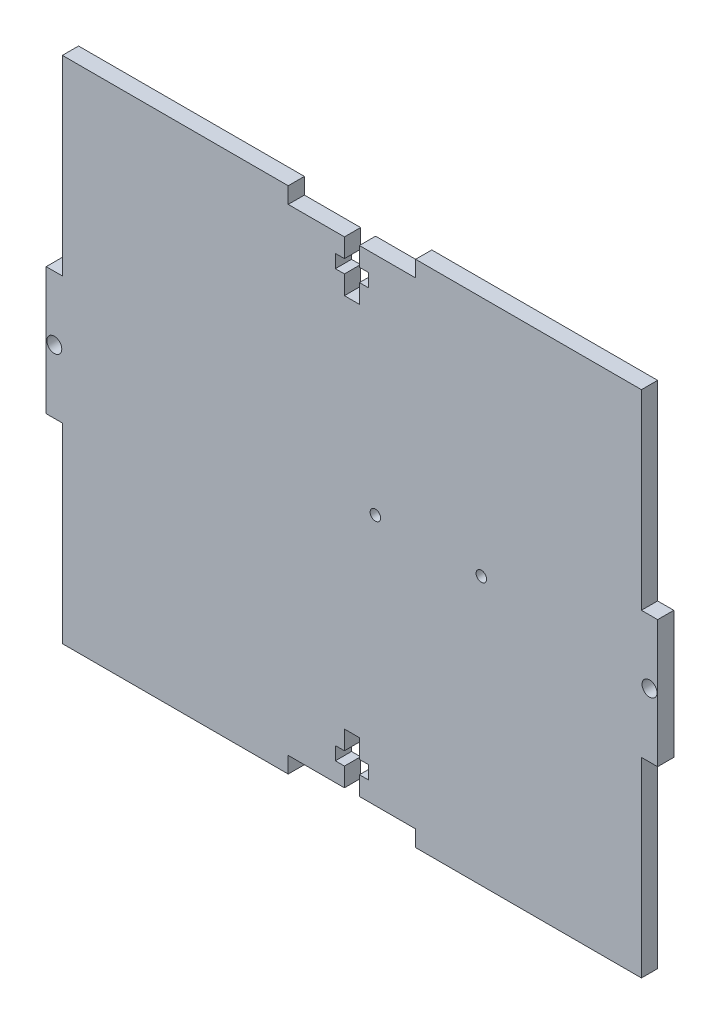
SolidWorks part; units mm, degrees
ref_plane "Front Plane" through (0, 0, 0) normal (0, 0, 1) x (1, 0, 0)
ref_plane "Top Plane" through (0, 0, 0) normal (0, 1, 0) x (1, 0, 0)
ref_plane "Right Plane" through (0, 0, 0) normal (1, 0, 0) x (0, 0, -1)
sketch "Sketch1" plane through (0, 0, 0) normal (0, 0, 1) x (1, 0, 0)
  line L0 (0, 50) -> (0, -50) construction
  line L1 (-56.825, 50) -> (56.825, 50)
  line L2 (-56.825, 50) -> (-56.825, -50)
  line L3 (-56.825, -50) -> (56.825, -50)
  line L4 (56.825, 50) -> (56.825, -50)
  line L5 (-56.825, 50) -> (56.825, -50) construction
  line L6 (-56.825, -50) -> (56.825, 50) construction
  line L7 (-56.825, 0) -> (56.825, 0) construction
  line L8 (-3.25, -40.525) -> (3.25, -40.525)
  line L9 (12.5, 50) -> (-12.5, 50)
  line L10 (12.5, 50) -> (12.5, 46.825)
  line L11 (12.5, 46.825) -> (-12.5, 46.825)
  line L12 (-12.5, 50) -> (-12.5, 46.825)
  line L13 (12.5, 50) -> (-12.5, 46.825) construction
  line L14 (12.5, 46.825) -> (-12.5, 50) construction
  line L15 (-1.47, 46.825) -> (1.47, 46.825)
  line L16 (-1.47, 46.825) -> (-1.47, 36.825)
  line L17 (-1.47, 36.825) -> (1.47, 36.825)
  line L18 (1.47, 46.825) -> (1.47, 36.825)
  line L19 (-1.47, 46.825) -> (1.47, 36.825) construction
  line L20 (-1.47, 36.825) -> (1.47, 46.825) construction
  line L21 (-3.25, 43.125) -> (3.25, 43.125)
  line L22 (-3.25, 43.125) -> (-3.25, 40.525)
  line L23 (-3.25, 40.525) -> (3.25, 40.525)
  line L24 (3.25, 43.125) -> (3.25, 40.525)
  line L25 (-3.25, 43.125) -> (3.25, 40.525) construction
  line L26 (-3.25, 40.525) -> (3.25, 43.125) construction
  line L27 (3.25, -43.125) -> (3.25, -40.525)
  line L28 (-3.25, -43.125) -> (3.25, -43.125)
  line L29 (-3.25, -43.125) -> (-3.25, -40.525)
  line L30 (-1.47, -36.825) -> (1.47, -36.825)
  line L31 (1.47, -46.825) -> (1.47, -36.825)
  line L32 (-1.47, -46.825) -> (1.47, -46.825)
  line L33 (-1.47, -46.825) -> (-1.47, -36.825)
  line L34 (12.5, -46.825) -> (-12.5, -46.825)
  line L35 (-12.5, -50) -> (-12.5, -46.825)
  line L36 (12.5, -50) -> (-12.5, -50)
  line L37 (12.5, -50) -> (12.5, -46.825)
  line L38 (60, -12.5) -> (56.825, -12.5)
  line L39 (-60, 12.5) -> (-56.825, 12.5)
  line L40 (-60, 12.5) -> (-60, -12.5)
  line L41 (-60, -12.5) -> (-56.825, -12.5)
  line L42 (-56.825, 12.5) -> (-56.825, -12.5)
  line L43 (-60, 12.5) -> (-56.825, -12.5) construction
  line L44 (-60, -12.5) -> (-56.825, 12.5) construction
  line L45 (56.825, 12.5) -> (56.825, -12.5)
  line L46 (60, 12.5) -> (56.825, 12.5)
  line L47 (60, 12.5) -> (60, -12.5)
  circle A0 centre (-58.4125, 0) radius 1.47
  circle A1 centre (58.4125, 0) radius 1.47
  circle A3 centre (25.4, 2.575) radius 1.0287
  circle A4 centre (4.6, 2.575) radius 1.0287
  point P0 (0, 0)
  point P10 (0, 48.4125)
  point P15 (0, 41.825)
  point P20 (0, 41.825)
  point P37 (-58.4125, 0)
  dimension "D11" = 2.94
  dimension "D1" = 100
  dimension "D2" = 113.65
  dimension "D3" = 3.175
  dimension "D4" = 10
  dimension "D5" = 2.94
  dimension "D6" = 25
  dimension "D7" = 6.5
  dimension "D8" = 2.6
  dimension "D9" = 6.3
  dimension "D10" = 3.175
extrude "Boss-Extrude1" add sketch "Sketch1" along normal mid plane 3.175 contours L21 L24 L23 L18 L17 L16 L22 L11 L12 L1 L2 L3 L4 L10 | L40 L39 L42 L41 | A0 | L38 L45 L46 L47 | A1
